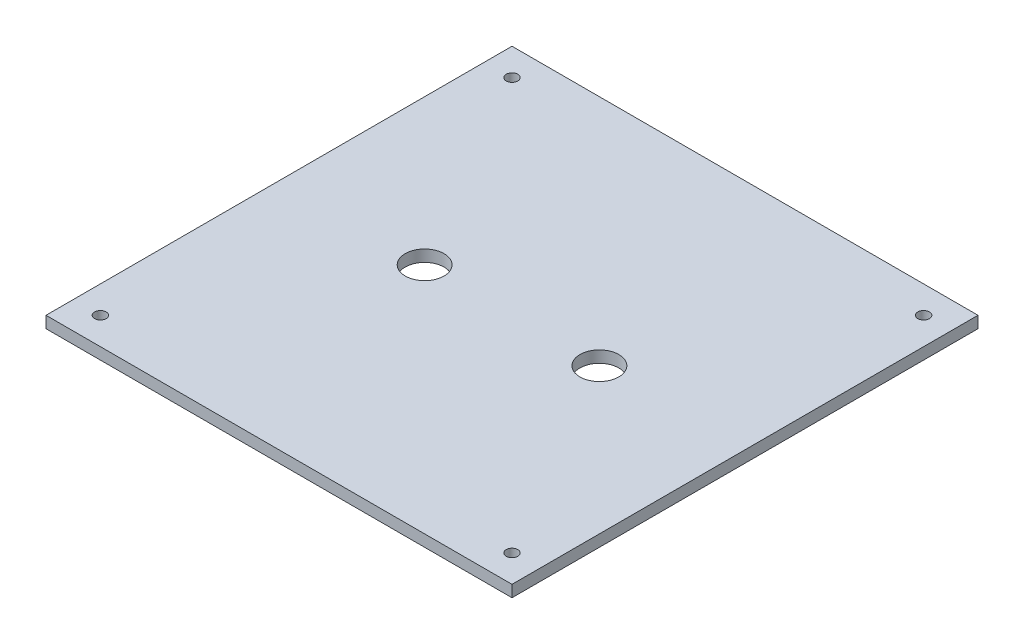
SolidWorks part; units mm, degrees
ref_plane "Front Plane" through (0, 0, 0) normal (0, 0, 1) x (1, 0, 0)
ref_plane "Top Plane" through (0, 0, 0) normal (0, 1, 0) x (1, 0, 0)
ref_plane "Right Plane" through (0, 0, 0) normal (1, 0, 0) x (0, 0, -1)
sketch "Sketch1" plane through (0, 0, 0) normal (0, 1, 0) x (1, 0, 0)
  line L1 (-60, -60) -> (60, -60)
  line L2 (-60, -60) -> (-60, 60)
  line L3 (-60, 60) -> (60, 60)
  line L4 (60, -60) -> (60, 60)
  line L5 (-60, -60) -> (60, 60) construction
  line L6 (-60, 60) -> (60, -60) construction
  point P0 (0, 0)
extrude "Boss-Extrude1" add sketch "Sketch1" along normal blind 3
sketch "Sketch2" plane through (0, 0, 0) normal (0, 1, 0) x (1, 0, 0)
  line L0 (-26, 0) -> (-26, 56.4247) construction
  line L1 (26, 0) -> (26, 58.8481) construction
  line L2 (0, 0) -> (0, 57.0064) construction
  line L3 (-19, 0) -> (-19, 37.3668) construction
  line L4 (19, 0) -> (19, 22.4016) construction
  line L5 (0, 0) -> (62.369, 0) construction
  line L6 (-22.5, 0) -> (-22.5, 36.1696) construction
  line L7 (22.5, 0) -> (22.5, 30.9816) construction
  dimension "D1" = 26
  dimension "D2" = 26
  dimension "D3" = 3.5
  dimension "D4" = 3.5
  dimension "D5" = 7
  dimension "D6" = 7
ref_point "Point1"
ref_point "Point2"
sketch "Sketch4" plane through (0, 0, 0) normal (0, 1, 0) x (1, 0, 0)
  circle A0 centre (-22.5, 0) radius 5
  circle A1 centre (22.5, 0) radius 5
extrude "Cut-Extrude2" cut sketch "Sketch4" along normal up to surface (3 mm away) up to face at (0, 3, 0)
sketch "Sketch5" plane through (0, 0, 0) normal (0, 1, 0) x (1, 0, 0)
  line L0 (-53, 0) -> (-53, 74.8856) construction
  line L1 (-55.2997, 53) -> (111.0551, 53) construction
  line L2 (53, 55.042) -> (53, 97.6787) construction
  line L3 (-55.2997, -53) -> (133.2261, -53) construction
  line L4 (-60, 60) -> (-60, -60) construction
  line L5 (60, -60) -> (60, 60) construction
  line L6 (-60, -60) -> (60, -60) construction
  line L7 (60, 60) -> (-60, 60) construction
  dimension "D1" = 7
  dimension "D2" = 7
  dimension "D3" = 7
  dimension "D4" = 7
ref_point "Point3"
ref_point "Point4"
ref_point "Point5"
ref_point "Point6"
sketch "Sketch7" plane through (0, 0, 0) normal (0, 1, 0) x (1, 0, 0)
  line L0 (-53, -200000) -> (-53, 200074.8856) construction
  line L1 (-200055.2997, -53) -> (200133.2261, -53) construction
  line L2 (53, -199944.958) -> (53, 200097.6787) construction
  circle A0 centre (-53, 53) radius 1.5
  circle A1 centre (53, 53) radius 1.5
  circle A2 centre (-53, -53) radius 1.5
  circle A3 centre (53, -53) radius 1.5
extrude "Cut-Extrude3" cut sketch "Sketch7" along normal up to surface (3 mm away) up to face at (-22.5, 3, -5)
